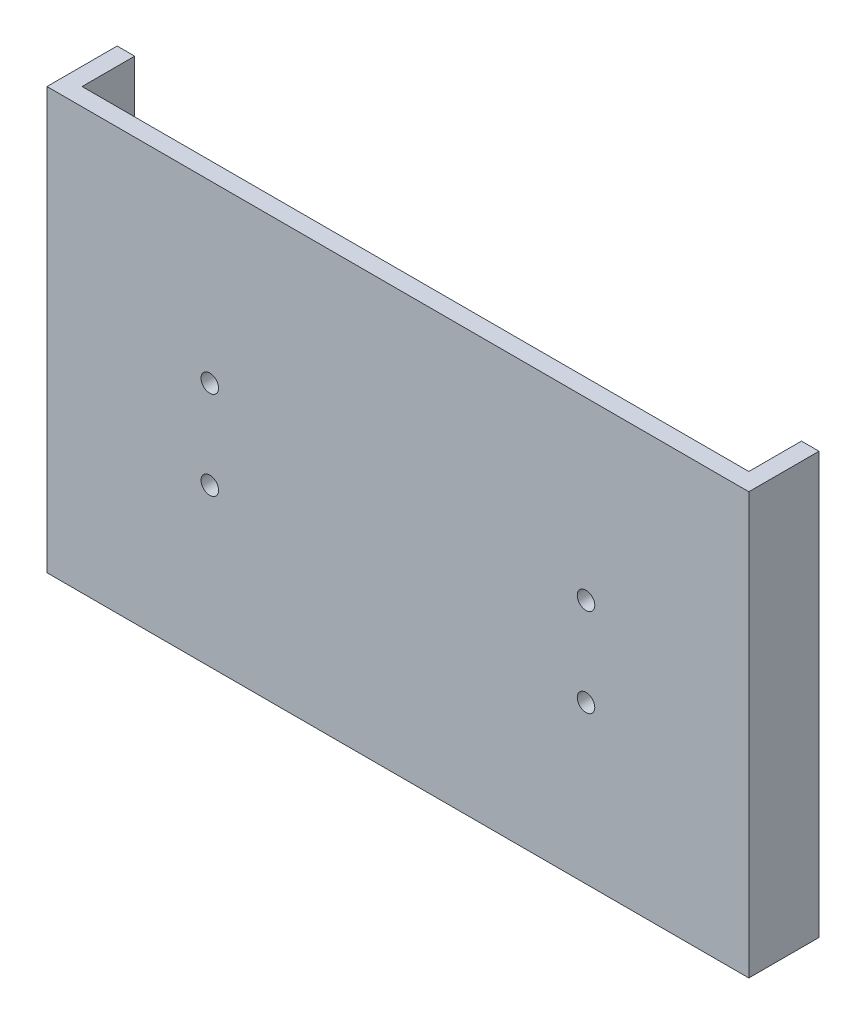
SolidWorks part; units mm, degrees
material "1060 Alloy"
ref_plane "Front Plane" through (0, 0, 0) normal (0, 0, 1) x (1, 0, 0)
ref_plane "Top Plane" through (0, 0, 0) normal (0, 1, 0) x (1, 0, 0)
ref_plane "Right Plane" through (0, 0, 0) normal (1, 0, 0) x (0, 0, -1)
sketch "Sketch2" plane through (0, 0, 0) normal (0, 1, 0) x (1, 0, 0)
  line L0 (0, 0) -> (0, 12.7)
  line L1 (0, 12.7) -> (3.175, 12.7)
  line L2 (3.175, 12.7) -> (3.175, 3.175)
  line L3 (3.175, 3.175) -> (123.825, 3.175)
  line L4 (123.825, 3.175) -> (123.825, 12.7)
  line L5 (123.825, 12.7) -> (127, 12.7)
  line L6 (127, 12.7) -> (127, 0)
  line L7 (127, 0) -> (0, 0)
  dimension "D1" = 127
  dimension "D2" = 12.7
  dimension "D3" = 3.175
  dimension "D4" = 9.525
extrude "Boss-Extrude1" add sketch "Sketch2" along normal blind 139.7
sketch "Sketch3" plane through (0, 0, -3.175) normal (0, 0, -1) x (-1, 0, 0)
  line L0 (-97.536, 91.948) -> (-29.464, 91.948) construction
  line L3 (-29.464, 91.948) -> (-29.464, 107.95) construction
  line L6 (-29.464, 107.95) -> (-97.536, 107.95) construction
  line L7 (-97.536, 107.95) -> (-97.536, 91.948) construction
  line L8 (-63.5, 139.7) -> (-63.5, 107.95) construction
  line L9 (0, 139.7) -> (0, 0) construction
  line L10 (-123.825, 139.7) -> (-3.175, 139.7) construction
  line L11 (-127, 139.7) -> (-127, 0) construction
  line L25 (0, 63.5) -> (0, 0)
  line L26 (0, 0) -> (-127, 0)
  line L27 (-127, 0) -> (-127, 63.5)
  line L28 (-127, 63.5) -> (0, 63.5)
  circle A4 centre (-97.536, 107.95) radius 1.5875
  circle A5 centre (-29.464, 107.95) radius 1.5875
  circle A6 centre (-29.464, 91.948) radius 1.5875
  circle A7 centre (-97.536, 91.948) radius 1.5875
  dimension "D2" = 31.75
  dimension "D1" = 3.175
  dimension "D3" = 68.072
  dimension "D4" = 16.002
  dimension "D6" = 63.5
extrude "Cut-Extrude1" cut sketch "Sketch3" against normal through all both and the other way through all
